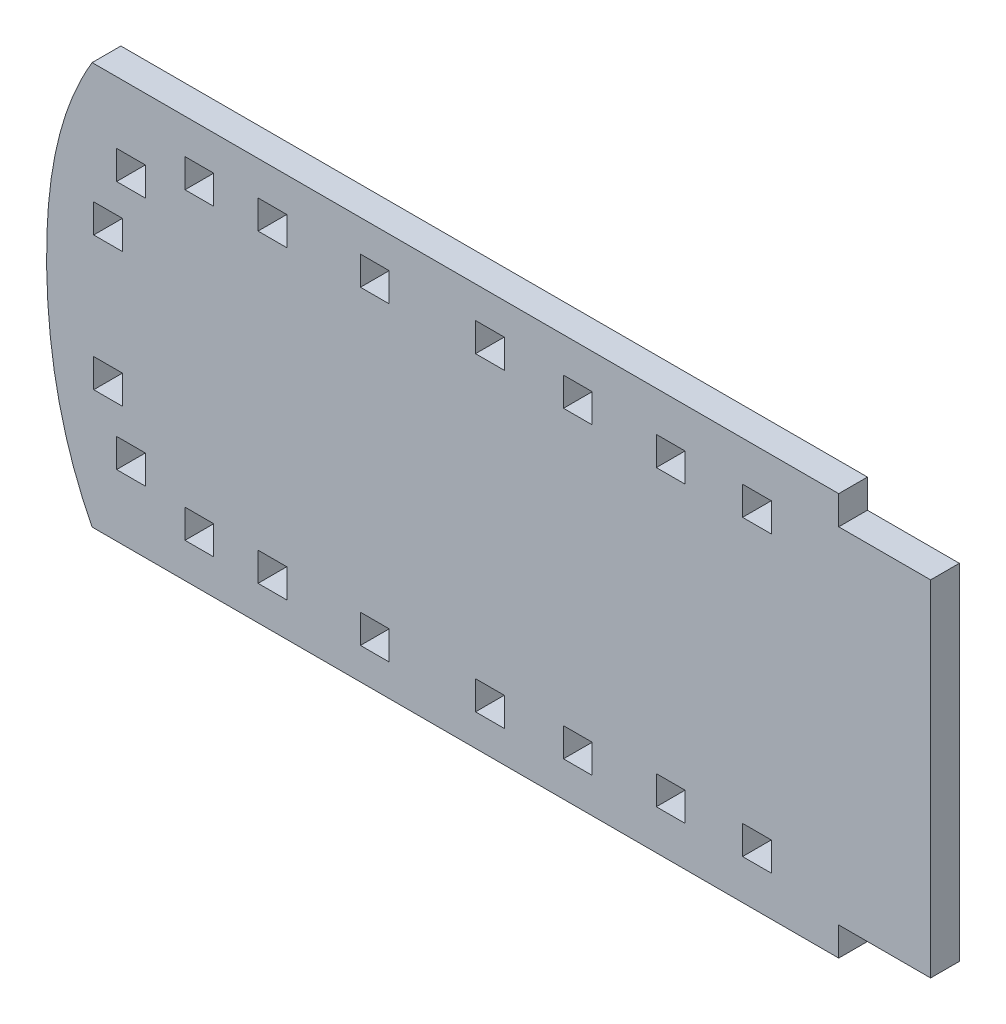
SolidWorks part; units mm, degrees
ref_plane "Front Plane" through (0, 0, 0) normal (0, 0, 1) x (1, 0, 0)
ref_plane "Top Plane" through (0, 0, 0) normal (0, 1, 0) x (1, 0, 0)
ref_plane "Right Plane" through (0, 0, 0) normal (1, 0, 0) x (0, 0, -1)
sketch "Sketch1" plane through (0, 0, 0) normal (0, 0, 1) x (1, 0, 0)
  line L0 (133.3535, 0) -> (218.4386, 0)
  line L1 (218.4386, 0) -> (218.4386, -3.175)
  line L2 (218.4386, -3.175) -> (228.5935, -3.175)
  line L4 (138.5382, -3.175) -> (308.2876, -3.175) construction
  line L5 (228.5935, -3.175) -> (228.5935, -41.275)
  line L6 (218.4386, -41.275) -> (228.5935, -41.275)
  line L7 (308.2876, -41.275) -> (138.5382, -41.275) construction
  line L8 (218.4386, -41.275) -> (218.4386, -44.45)
  line L9 (218.4386, -44.45) -> (133.3535, -44.45)
  spline S0 degree 3 poles (133.3535, 0) (129.67, -3.8041) (126.1278, -11.4604) (125.7176, -27.473) (126.7428, -38.6419) (133.3535, -44.45) knots 0 0 0 0 0.328356 0.501119 1 1 1 1
extrude "Boss-Extrude1" add sketch "Sketch1" along normal blind 3.175 contours S0 L9 L8 L6 L5 L2 L1 L0
sketch "Sketch2" plane through (0, 0, 3.175) normal (0, 0, 1) x (1, 0, 0)
  line L0 (133.3535, 0) -> (218.4386, 0) construction
  line L1 (218.4386, -44.45) -> (133.3535, -44.45) construction
  line L2 (135.9393, 0) -> (128.3366, 5.1863)
  line L3 (128.3366, 5.1863) -> (108.4783, -42.0961)
  line L4 (108.4783, -42.0961) -> (132.0917, -56.3708)
  line L5 (132.0917, -56.3708) -> (135.9393, -44.45)
  spline S0 degree 3 poles (135.9393, 0) (131.855, -6.8171) (129.6911, -22.3684) (132.4284, -37.6157) (135.9393, -44.45) knots 0 0 0 0 0.506943 1 1 1 1
extrude "Cut-Extrude1" cut sketch "Sketch2" against normal blind 3.175
sketch "Sketch3" plane through (0, 0, 3.175) normal (0, 0, 1) x (1, 0, 0)
  line L1 (136.1159, -28.0415) -> (139.2909, -28.0415)
  line L2 (136.1159, -28.0415) -> (136.1159, -31.2165)
  line L3 (136.1159, -31.2165) -> (139.2909, -31.2165)
  line L4 (139.2909, -28.0415) -> (139.2909, -31.2165)
  line L5 (136.1159, -28.0415) -> (139.2909, -31.2165) construction
  line L6 (136.1159, -31.2165) -> (139.2909, -28.0415) construction
  line L7 (138.6436, -34.4195) -> (141.8186, -34.4195)
  line L8 (138.6436, -34.4195) -> (138.6436, -37.5945)
  line L9 (138.6436, -37.5945) -> (141.8186, -37.5945)
  line L10 (141.8186, -34.4195) -> (141.8186, -37.5945)
  line L11 (138.6436, -34.4195) -> (141.8186, -37.5945) construction
  line L12 (138.6436, -37.5945) -> (141.8186, -34.4195) construction
  line L13 (154.273, -37.4921) -> (157.448, -37.4921)
  line L14 (154.273, -37.4921) -> (154.273, -40.6671)
  line L15 (154.273, -40.6671) -> (157.448, -40.6671)
  line L16 (157.448, -37.4921) -> (157.448, -40.6671)
  line L17 (154.273, -37.4921) -> (157.448, -40.6671) construction
  line L18 (154.273, -40.6671) -> (157.448, -37.4921) construction
  line L19 (146.2022, -40.586) -> (149.3772, -40.586)
  line L20 (146.2022, -40.586) -> (146.2022, -37.411)
  line L21 (146.2022, -37.411) -> (149.3772, -37.411)
  line L22 (149.3772, -40.586) -> (149.3772, -37.411)
  line L23 (146.2022, -40.586) -> (149.3772, -37.411) construction
  line L24 (146.2022, -37.411) -> (149.3772, -40.586) construction
  line L25 (165.5907, -40.9501) -> (168.7657, -40.9501)
  line L26 (165.5907, -40.9501) -> (165.5907, -37.7751)
  line L27 (165.5907, -37.7751) -> (168.7657, -37.7751)
  line L28 (168.7657, -40.9501) -> (168.7657, -37.7751)
  line L29 (165.5907, -40.9501) -> (168.7657, -37.7751) construction
  line L30 (165.5907, -37.7751) -> (168.7657, -40.9501) construction
  line L31 (178.3045, -40.9501) -> (181.4795, -40.9501)
  line L32 (178.3045, -40.9501) -> (178.3045, -37.7751)
  line L33 (178.3045, -37.7751) -> (181.4795, -37.7751)
  line L34 (181.4795, -40.9501) -> (181.4795, -37.7751)
  line L35 (178.3045, -40.9501) -> (181.4795, -37.7751) construction
  line L36 (178.3045, -37.7751) -> (181.4795, -40.9501) construction
  line L37 (188.0255, -40.586) -> (191.2005, -40.586)
  line L38 (188.0255, -40.586) -> (188.0255, -37.411)
  line L39 (188.0255, -37.411) -> (191.2005, -37.411)
  line L40 (191.2005, -40.586) -> (191.2005, -37.411)
  line L41 (188.0255, -40.586) -> (191.2005, -37.411) construction
  line L42 (188.0255, -37.411) -> (191.2005, -40.586) construction
  line L43 (198.2852, -40.0423) -> (201.4602, -40.0423)
  line L44 (198.2852, -40.0423) -> (198.2852, -36.8673)
  line L45 (198.2852, -36.8673) -> (201.4602, -36.8673)
  line L46 (201.4602, -40.0423) -> (201.4602, -36.8673)
  line L47 (198.2852, -40.0423) -> (201.4602, -36.8673) construction
  line L48 (198.2852, -36.8673) -> (201.4602, -40.0423) construction
  line L49 (207.8141, -40.0423) -> (210.9891, -40.0423)
  line L50 (207.8141, -40.0423) -> (207.8141, -36.8673)
  line L51 (207.8141, -36.8673) -> (210.9891, -36.8673)
  line L52 (210.9891, -40.0423) -> (210.9891, -36.8673)
  line L53 (207.8141, -40.0423) -> (210.9891, -36.8673) construction
  line L54 (207.8141, -36.8673) -> (210.9891, -40.0423) construction
  line L55 (228.5935, -22.225) -> (130.9153, -22.225)
  line L57 (207.8141, -7.5827) -> (210.9891, -4.4077) construction
  line L58 (207.8141, -4.4077) -> (210.9891, -7.5827) construction
  line L59 (198.2852, -7.5827) -> (201.4602, -4.4077) construction
  line L60 (198.2852, -4.4077) -> (201.4602, -7.5827) construction
  line L61 (188.0255, -7.039) -> (191.2005, -3.864) construction
  line L62 (188.0255, -3.864) -> (191.2005, -7.039) construction
  line L63 (178.3045, -6.6749) -> (181.4795, -3.4999) construction
  line L64 (178.3045, -3.4999) -> (181.4795, -6.6749) construction
  line L65 (165.5907, -6.6749) -> (168.7657, -3.4999) construction
  line L66 (165.5907, -3.4999) -> (168.7657, -6.6749) construction
  line L67 (146.2022, -7.039) -> (149.3772, -3.864) construction
  line L68 (146.2022, -3.864) -> (149.3772, -7.039) construction
  line L69 (154.273, -3.7829) -> (157.448, -6.9579) construction
  line L70 (154.273, -6.9579) -> (157.448, -3.7829) construction
  line L71 (138.6436, -6.8555) -> (141.8186, -10.0305) construction
  line L72 (138.6436, -10.0305) -> (141.8186, -6.8555) construction
  line L73 (136.1159, -13.2335) -> (139.2909, -16.4085) construction
  line L74 (136.1159, -16.4085) -> (139.2909, -13.2335) construction
  line L75 (210.9891, -4.4077) -> (210.9891, -7.5827)
  line L76 (207.8141, -7.5827) -> (210.9891, -7.5827)
  line L77 (207.8141, -4.4077) -> (207.8141, -7.5827)
  line L78 (207.8141, -4.4077) -> (210.9891, -4.4077)
  line L79 (201.4602, -4.4077) -> (201.4602, -7.5827)
  line L80 (198.2852, -7.5827) -> (201.4602, -7.5827)
  line L81 (198.2852, -4.4077) -> (198.2852, -7.5827)
  line L82 (198.2852, -4.4077) -> (201.4602, -4.4077)
  line L83 (191.2005, -3.864) -> (191.2005, -7.039)
  line L84 (188.0255, -7.039) -> (191.2005, -7.039)
  line L85 (188.0255, -3.864) -> (188.0255, -7.039)
  line L86 (188.0255, -3.864) -> (191.2005, -3.864)
  line L87 (181.4795, -3.4999) -> (181.4795, -6.6749)
  line L88 (178.3045, -6.6749) -> (181.4795, -6.6749)
  line L89 (178.3045, -3.4999) -> (178.3045, -6.6749)
  line L90 (178.3045, -3.4999) -> (181.4795, -3.4999)
  line L91 (168.7657, -3.4999) -> (168.7657, -6.6749)
  line L92 (165.5907, -6.6749) -> (168.7657, -6.6749)
  line L93 (165.5907, -3.4999) -> (165.5907, -6.6749)
  line L94 (165.5907, -3.4999) -> (168.7657, -3.4999)
  line L95 (149.3772, -3.864) -> (149.3772, -7.039)
  line L96 (146.2022, -7.039) -> (149.3772, -7.039)
  line L97 (146.2022, -3.864) -> (146.2022, -7.039)
  line L98 (146.2022, -3.864) -> (149.3772, -3.864)
  line L99 (157.448, -6.9579) -> (157.448, -3.7829)
  line L100 (154.273, -3.7829) -> (157.448, -3.7829)
  line L101 (154.273, -6.9579) -> (154.273, -3.7829)
  line L102 (154.273, -6.9579) -> (157.448, -6.9579)
  line L103 (141.8186, -10.0305) -> (141.8186, -6.8555)
  line L104 (138.6436, -6.8555) -> (141.8186, -6.8555)
  line L105 (138.6436, -10.0305) -> (138.6436, -6.8555)
  line L106 (138.6436, -10.0305) -> (141.8186, -10.0305)
  line L107 (139.2909, -16.4085) -> (139.2909, -13.2335)
  line L108 (136.1159, -13.2335) -> (139.2909, -13.2335)
  line L109 (136.1159, -16.4085) -> (136.1159, -13.2335)
  line L110 (136.1159, -16.4085) -> (139.2909, -16.4085)
  line L111 (228.5935, -3.175) -> (228.5935, -41.275) construction
  spline S0 degree 3 poles (135.9393, -44.45) (132.4284, -37.6157) (129.6911, -22.3684) (131.855, -6.8171) (135.9393, 0) knots 0 0 0 0 0.493057 1 1 1 1 construction
  point P0 (137.7034, -29.629)
  point P5 (140.2311, -36.007)
  point P10 (148.2565, -37.8755)
  point P15 (147.7897, -38.9985)
  point P20 (167.1782, -39.3626)
  point P25 (179.892, -39.3626)
  point P30 (189.613, -38.9985)
  point P35 (199.8727, -38.4548)
  point P40 (209.4016, -38.4548)
  point P89 (209.4016, -5.9952)
  point P90 (199.8727, -5.9952)
  point P91 (189.613, -5.4515)
  point P92 (179.892, -5.0874)
  point P93 (167.1782, -5.0874)
  point P94 (147.7897, -5.4515)
  point P95 (148.2565, -6.5745)
  point P96 (140.2311, -8.443)
  point P97 (137.7034, -14.821)
  dimension "D1" = 3.175
  dimension "D2" = 3.175
  dimension "D3" = 3.175
  dimension "D4" = 3.175
  dimension "D5" = 3.175
  dimension "D6" = 3.175
  dimension "D7" = 3.175
  dimension "D8" = 3.175
  dimension "D9" = 3.175
extrude "Cut-Extrude2" cut sketch "Sketch3" against normal blind 3.175 contours L105 L106 L103 L104 | L101 L102 L99 L100 | L98 L97 L96 L95 | L94 L93 L92 L91 | L90 L89 L88 L87 | L86 L85 L84 L83 | L82 L81 L80 L79 | L49 L52 L51 L50 | L43 L46 L45 L44 | L37 L40 L39 L38 | L31 L34 L33 L32 | L25 L28 L27 L26 | L19 L22 L21 L20 | L16 L13 L14 L15 | L10 L7 L8 L9 | L4 L1 L2 L3 | L109 L110 L107 L108 | L78 L75 L76 L77
